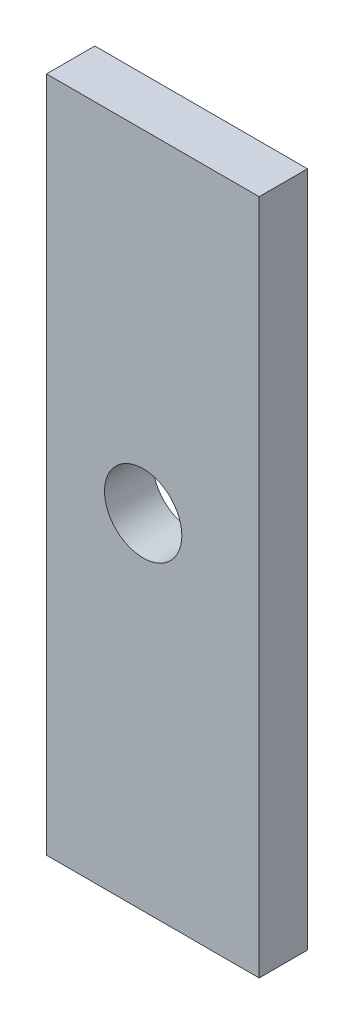
SolidWorks part; units mm, degrees
ref_plane "Front Plane" through (0, 0, 0) normal (0, 0, 1) x (1, 0, 0)
ref_plane "Top Plane" through (0, 0, 0) normal (0, 1, 0) x (1, 0, 0)
ref_plane "Right Plane" through (0, 0, 0) normal (1, 0, 0) x (0, 0, -1)
sketch "Sketch1" plane through (0, 0, 0) normal (0, 0, 1) x (1, 0, 0)
  line L1 (-75, -35) -> (75, -35)
  line L2 (-75, -35) -> (-75, 35)
  line L3 (-75, 35) -> (75, 35)
  line L4 (75, -35) -> (75, 35)
  line L5 (-75, -35) -> (75, 35) construction
  line L6 (-75, 35) -> (75, -35) construction
  point P0 (0, 0)
  dimension "D1" = 150
  dimension "D2" = 70
extrude "Boss-Extrude1" add sketch "Sketch1" along normal mid plane 5
sketch "Sketch2" plane through (0, 0, 2.5) normal (0, 0, 1) x (1, 0, 0)
  circle A0 centre (63, 0.6285) radius 4
  circle A1 centre (29.0015, 0.3096) radius 4
  circle A2 centre (-42.9953, -0.3659) radius 4
  circle A3 centre (-3.9971, 0) radius 4
  dimension "D1" = 8
  dimension "D2" = 8
  dimension "D3" = 8
  dimension "D4" = 8
extrude "Cut-Extrude1" cut sketch "Sketch2" against normal through all
sketch "Sketch3" plane through (0, 0, -2.5) normal (0, 0, -1) x (-1, 0, 0)
  line L0 (-75, 35) -> (75, 35) construction
  line L1 (75, -35) -> (-45, -35)
  line L2 (75, -35) -> (75, 35)
  line L3 (75, 35) -> (-45, 35)
  line L4 (-45, -35) -> (-45, 35)
  dimension "D1" = 120
extrude "Cut-Extrude2" cut sketch "Sketch3" against normal through all contours L4 L3 L2 L1
sketch "Sketch4" plane through (0, 0, -2.5) normal (0, 0, -1) x (-1, 0, 0)
  line L0 (-75, 35) -> (-45, 35) construction
  line L1 (-45, -35) -> (-53, -35)
  line L2 (-45, -35) -> (-45, 35)
  line L3 (-45, 35) -> (-53, 35)
  line L4 (-53, -35) -> (-53, 35)
  dimension "D1" = 8
extrude "Cut-Extrude3" cut sketch "Sketch4" against normal through all
